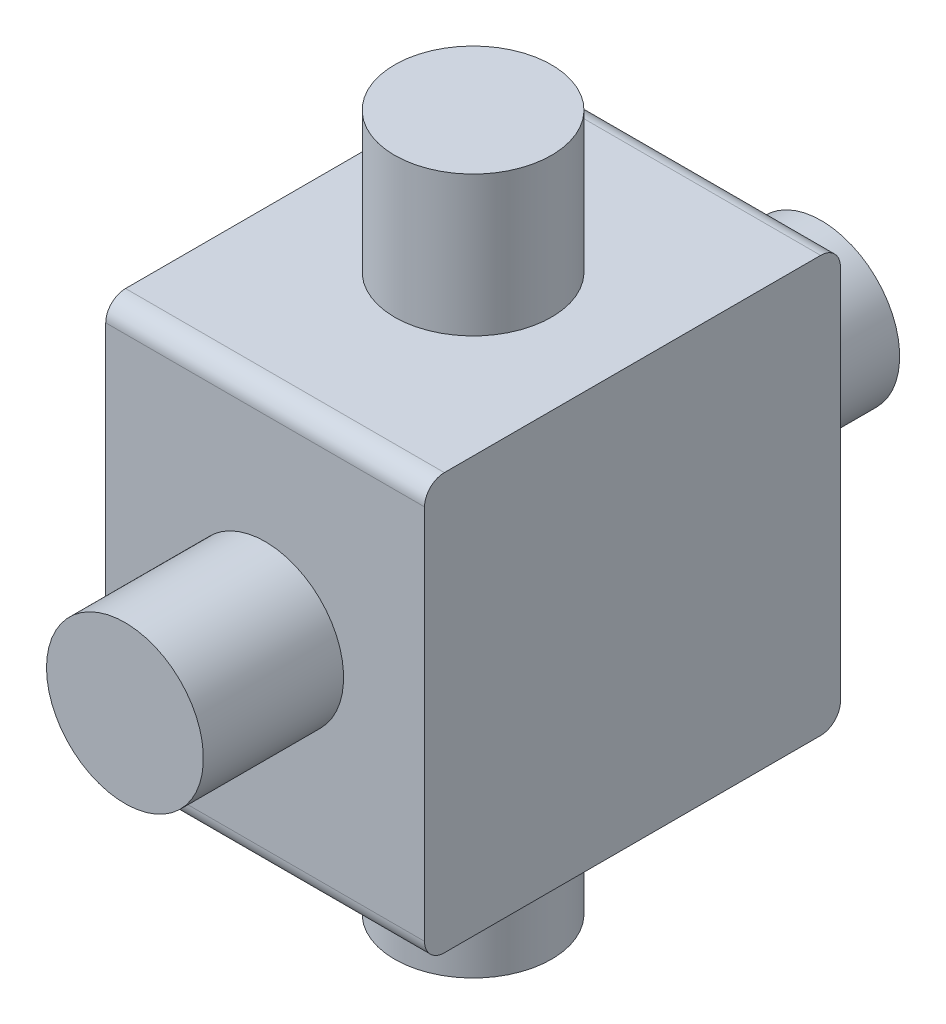
SolidWorks part; units mm, degrees
ref_plane "Płaszczyzna XY" through (0, 0, 0) normal (0, 0, 1) x (1, 0, 0)
ref_plane "Płaszczyzna XZ" through (0, 0, 0) normal (0, 1, 0) x (1, 0, 0)
ref_plane "Płaszczyzna YZ" through (0, 0, 0) normal (1, 0, 0) x (0, 0, -1)
ref_plane "Płaszczyzna1" through (5.06, 0, 0) normal (1, 0, 0) x (0, 0, -1)
sketch "Szkic1" plane through (5.06, 0, 0) normal (1, 0, 0) x (0, 0, -1)
  line L0 (-6.6, 6.6) -> (-6.6, -6.6)
  line L1 (-6.6, -6.6) -> (6.6, -6.6)
  line L2 (6.6, -6.6) -> (6.6, 6.6)
  line L3 (6.6, 6.6) -> (-6.6, 6.6)
extrude "Dodanie-wyciągnięcie1" add sketch "Szkic1" against normal blind 10.12
ref_plane "Płaszczyzna2" through (0, 0, 0) normal (0, 0, -1) x (-1, 0, 0)
sketch "Szkic2" plane through (0, 0, 0) normal (0, 0, -1) x (-1, 0, 0)
  line L0 (-2.49, 6.6) -> (0, 6.6)
  line L1 (0, 6.6) -> (0, 11.05)
  line L2 (0, 11.05) -> (-2.49, 11.05)
  line L3 (-2.49, 11.05) -> (-2.49, 6.6)
  line L4 (0, 6.6) -> (0, 11.05) construction
revolve "Obrót1" add sketch "Szkic2" angle 360 about L4
ref_plane "Płaszczyzna3" through (0, 0, 0) normal (0, -1, 0) x (1, 0, 0)
sketch "Szkic3" plane through (0, 0, 0) normal (0, -1, 0) x (1, 0, 0)
  line L0 (2.49, -6.6) -> (0, -6.6)
  line L1 (0, -6.6) -> (0, -11.05)
  line L2 (0, -11.05) -> (2.49, -11.05)
  line L3 (2.49, -11.05) -> (2.49, -6.6)
  line L4 (0, -6.6) -> (0, -11.05) construction
revolve "Obrót2" add sketch "Szkic3" angle 360 about L4
sketch "Szkic4" plane through (0, 0, 0) normal (0, 0, -1) x (-1, 0, 0)
  line L0 (-2.49, -11.05) -> (0, -11.05)
  line L1 (0, -11.05) -> (0, -6.6)
  line L2 (0, -6.6) -> (-2.49, -6.6)
  line L3 (-2.49, -6.6) -> (-2.49, -11.05)
  line L4 (0, -11.05) -> (0, -6.6) construction
revolve "Obrót3" add sketch "Szkic4" angle 360 about L4
sketch "Szkic5" plane through (0, 0, 0) normal (0, -1, 0) x (1, 0, 0)
  line L0 (2.49, 11.05) -> (0, 11.05)
  line L1 (0, 11.05) -> (0, 6.6)
  line L2 (0, 6.6) -> (2.49, 6.6)
  line L3 (2.49, 6.6) -> (2.49, 11.05)
  line L4 (0, 11.05) -> (0, 6.6) construction
revolve "Obrót4" add sketch "Szkic5" angle 360 about L4
fillet "Zaokrąglenie1" radius 0.6286 4 edges at (0, -6.6, 6.6) (0, -6.6, -6.6) (0, 6.6, 6.6) (0, 6.6, -6.6)
